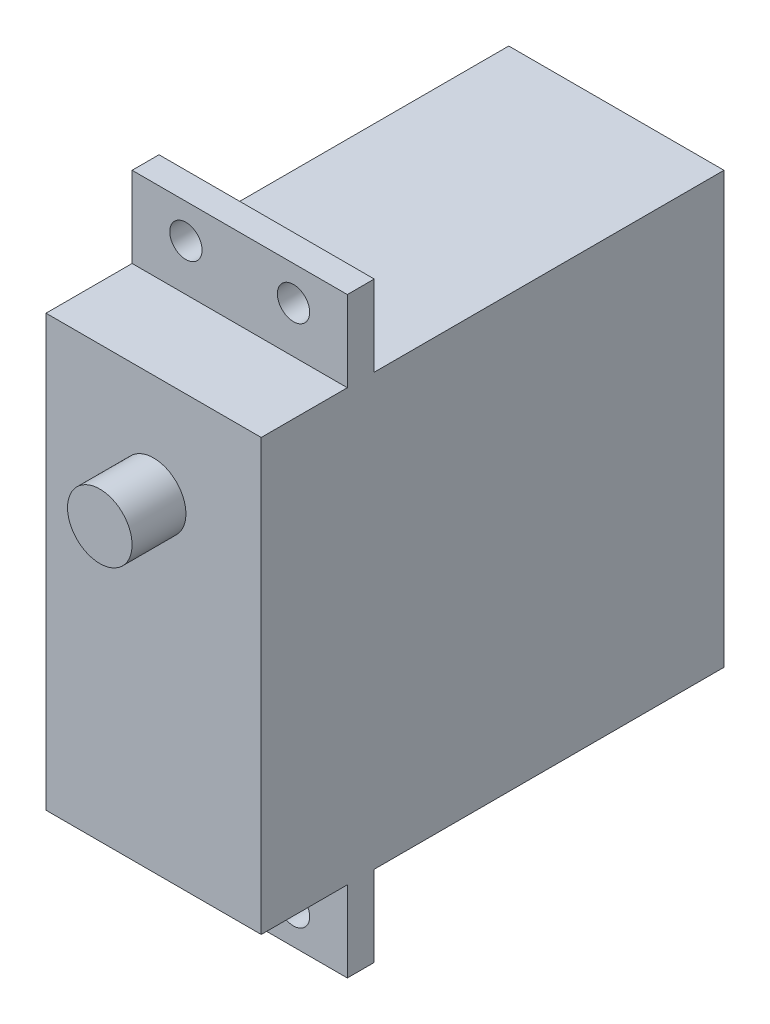
SolidWorks part; units mm, degrees
ref_plane "前视" through (0, 0, 0) normal (0, 0, 1) x (1, 0, 0)
ref_plane "上视" through (0, 0, 0) normal (0, 1, 0) x (1, 0, 0)
ref_plane "右视" through (0, 0, 0) normal (1, 0, 0) x (0, 0, -1)
sketch "草图1" plane through (0, 0, 0) normal (0, 0, 1) x (1, 0, 0)
  line L1 (-10, -20) -> (10, -20)
  line L2 (-10, -20) -> (-10, 20)
  line L3 (-10, 20) -> (10, 20)
  line L4 (10, -20) -> (10, 20)
  line L5 (-10, -20) -> (10, 20) construction
  line L6 (-10, 20) -> (10, -20) construction
  point P0 (0, 0)
  dimension "D1" = 40
  dimension "D2" = 20
extrude "凸台-拉伸1" add sketch "草图1" along normal blind 32.5
sketch "草图2" plane through (0, 0, 32.5) normal (0, 0, 1) x (1, 0, 0)
  line L1 (-10, -27.5) -> (10, -27.5)
  line L2 (-10, -27.5) -> (-10, 27.5)
  line L3 (-10, 27.5) -> (10, 27.5)
  line L4 (10, -27.5) -> (10, 27.5)
  line L5 (-10, -27.5) -> (10, 27.5) construction
  line L6 (-10, 27.5) -> (10, -27.5) construction
  point P0 (0, 0)
  dimension "D1" = 20
  dimension "D2" = 55
extrude "凸台-拉伸2" add sketch "草图2" along normal blind 2.5
sketch "草图3" plane through (0, 0, 35) normal (0, 0, 1) x (1, 0, 0)
  line L1 (-10, -20) -> (10, -20)
  line L2 (-10, -20) -> (-10, 20)
  line L3 (-10, 20) -> (10, 20)
  line L4 (10, -20) -> (10, 20)
  line L5 (-10, -20) -> (10, 20) construction
  line L6 (-10, 20) -> (10, -20) construction
  point P0 (0, 0)
  dimension "D1" = 20
  dimension "D2" = 40
extrude "凸台-拉伸3" add sketch "草图3" along normal blind 8
sketch "草图4" plane through (0, 0, 43) normal (0, 0, 1) x (1, 0, 0)
  line L0 (10, 27.5) -> (-10, 27.5) construction
  circle A0 centre (0, 10.35) radius 3
  dimension "D1" = 17.15
  dimension "D2" = 6
extrude "凸台-拉伸4" add sketch "草图4" along normal offset from surface (5 mm away) 48 up to face at (0, 0, 0)
sketch "草图5" plane through (0, 0, 35) normal (0, 0, 1) x (1, 0, 0)
  circle A0 centre (-5, 24.315) radius 1.5
  circle A1 centre (5, 24.315) radius 1.5
  circle A2 centre (-5, -24.315) radius 1.5
  circle A3 centre (5, -24.315) radius 1.5
  dimension "D1" = 10
  dimension "D2" = 10
  dimension "D3" = 5
  dimension "D4" = 48.63
  dimension "D5" = 24.315
extrude "切除-拉伸1" cut sketch "草图5" against normal through all
sketch "草图6" plane through (10, 0, 0) normal (1, 0, 0) x (0, 0, -1)
  line L1 (-39.5, 20.15) -> (-38, 20.15)
  line L2 (-39.5, 20.15) -> (-39.5, 15.15)
  line L3 (-39.5, 15.15) -> (-38, 15.15)
  line L4 (-38, 20.15) -> (-38, 15.15)
  line L5 (-39.5, -20.15) -> (-38, -20.15)
  line L6 (-39.5, -20.15) -> (-39.5, -15.15)
  line L7 (-39.5, -15.15) -> (-38, -15.15)
  line L8 (-38, -20.15) -> (-38, -15.15)
  line L9 (-35, -27.5) -> (-35, -20) construction
  line L10 (-35, 20) -> (-35, 27.5) construction
  dimension "D1" = 3
  dimension "D2" = 3
  dimension "D3" = 5
  dimension "D4" = 5
